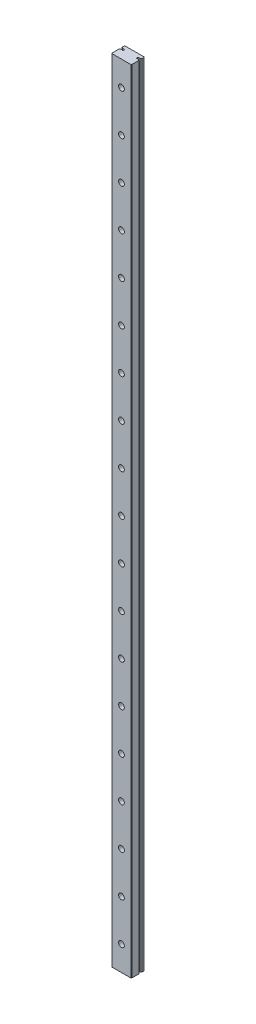
SolidWorks part; units mm, degrees
ref_plane "Front Plane" through (0, 0, 0) normal (0, 0, 1) x (1, 0, 0)
ref_plane "Top Plane" through (0, 0, 0) normal (0, 1, 0) x (1, 0, 0)
ref_plane "Right Plane" through (0, 0, 0) normal (1, 0, 0) x (0, 0, -1)
ref_plane "Plane1" through (0, 0, -4) normal (0, 0, -1) x (-1, 0, 0)
sketch "Sketch1" plane through (0, 0, -4) normal (0, 0, -1) x (-1, 0, 0)
  line L0 (-5.9695, 0) -> (6.0305, 0)
  line L1 (6.0305, 0) -> (6.0305, 480)
  line L2 (6.0305, 480) -> (-5.9695, 480)
  line L3 (-5.9695, 480) -> (-5.9695, 0)
extrude "Boss-Extrude1" add sketch "Sketch1" against normal blind 8
sketch "Sketch2" plane through (0, 480, 0) normal (0, 1, 0) x (-1, 0, 0)
  line L0 (6.0305, -2.4577) -> (6.0305, -1.0033)
  line L1 (6.0305, -1.0033) -> (4.0489, -1.0033)
  line L2 (4.0489, -1.0033) -> (4.0489, -1.9939)
  line L3 (4.0489, -1.9939) -> (5.4205, -1.9939)
  arc A0 (5.4205, -1.9939) -> (6.0305, -2.4577) centre (6.2784, -1.4986) ccw
extrude "Cut-Extrude1" cut sketch "Sketch2" against normal through all
sketch "Sketch3" plane through (0, 480, 0) normal (0, 1, 0) x (-1, 0, 0)
  line L0 (-5.9695, -1.0033) -> (-5.9695, -2.4577)
  line L1 (-5.3594, -1.9939) -> (-3.9878, -1.9939)
  line L2 (-3.9878, -1.9939) -> (-3.9878, -1.0033)
  line L3 (-3.9878, -1.0033) -> (-5.9695, -1.0033)
  arc A0 (-5.9695, -2.4577) -> (-5.3594, -1.9939) centre (-6.2173, -1.4986) ccw
extrude "Cut-Extrude2" cut sketch "Sketch3" against normal through all
sketch "Sketch4" plane through (0, 480, 0) normal (0, 1, 0) x (-1, 0, 0)
  line L0 (-5.9695, -1.0033) -> (-5.3594, -1.0033)
  line L1 (-5.9695, -0.5395) -> (-5.9695, -1.0033)
  arc A0 (-5.3594, -1.0033) -> (-5.9695, -0.5395) centre (-6.2173, -1.4986) ccw
extrude "Cut-Extrude3" cut sketch "Sketch4" against normal through all
sketch "Sketch5" plane through (0, 480, 0) normal (0, 1, 0) x (-1, 0, 0)
  line L0 (6.0305, -1.0033) -> (6.0305, -0.5395)
  line L1 (5.4205, -1.0033) -> (6.0305, -1.0033)
  arc A0 (6.0305, -0.5395) -> (5.4205, -1.0033) centre (6.2784, -1.4986) ccw
extrude "Cut-Extrude4" cut sketch "Sketch5" against normal through all
hole_wizard "CBORE for M3 Hex Head Machine Screw1" positions "Sketch7" profile "Sketch6" counterbore size "M3" standard "ANSI Metric"
sketch "Sketch7" plane through (0, 0, -4) normal (0, 0, -1) x (-1, 0, 0)
  point P0 (0, 465)
  point P1 (0, 440)
  point P2 (0, 415)
  point P3 (0, 390)
  point P4 (0, 365)
  point P5 (0, 340)
  point P6 (0, 315)
  point P7 (0, 290)
  point P8 (0, 265)
  point P9 (0, 240)
  point P10 (0, 215)
  point P11 (0, 190)
  point P12 (0, 165)
  point P13 (0, 140)
  point P14 (0, 115)
  point P15 (0, 90)
  point P16 (0, 65)
  point P17 (0, 40)
  point P18 (0, 15)
sketch "Sketch6" plane through (0, 465, -4) normal (1, 0, 0) x (0, 1, 0)
  line L0 (0, 0) -> (0, 8)
  line L1 (0, 8) -> (1.75, 8)
  line L3 (1.75, 8) -> (1.75, 4.5)
  line L4 (1.75, 4.5) -> (3, 4.5)
  line L5 (3, 4.5) -> (3, 0)
  line L7 (3, 0) -> (0, 0)
  line L11 (0, -6.35) -> (0, 107.95) construction
  dimension "Thru Hole Dia." = 3.5
  dimension "Thru Hole Depth" = 8
  dimension "C'Bore Dia." = 6
  dimension "C'Bore Depth" = 4.5
chamfer "Chamfer1" distance 0.5 angle 45 19 edges at (-3, 190, -4) (-3, 90, -4) (-3, 240, -4) (-3, 140, -4) (-3, 40, -4) (-3, 465, -4) (-3, 265, -4) (-3, 440, -4) (-3, 215, -4) (-3, 415, -4) (-3, 165, -4) (-3, 390, -4) (-3, 115, -4) (-3, 365, -4) (-3, 65, -4) (-3, 340, -4) (-3, 15, -4) (-3, 315, -4) (-3, 290, -4)
chamfer "Chamfer2" distance 0.2977 angle 45 4 edges at (-6.0305, 240, -4) (5.9695, 240, -4) (5.9695, 240, 4) (-6.0305, 240, 4)
